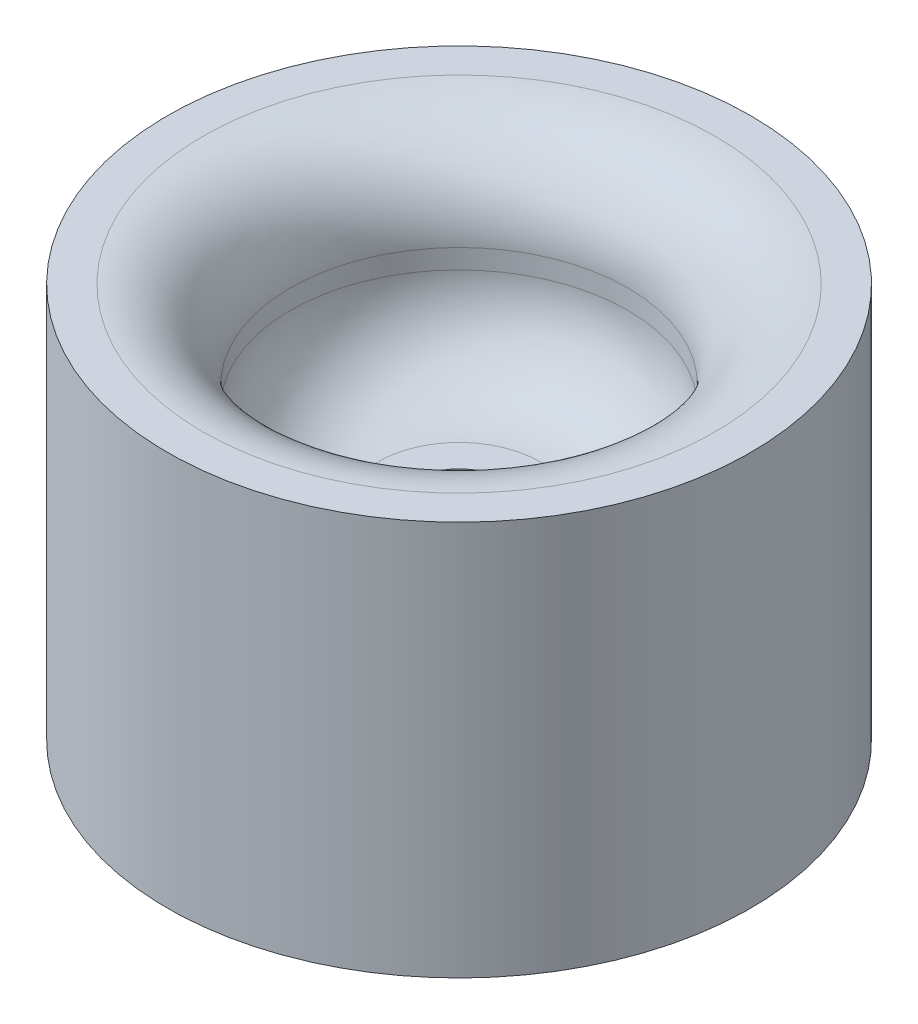
SolidWorks part; units mm, degrees
ref_plane "Front Plane" through (0, 0, 0) normal (0, 0, 1) x (1, 0, 0)
ref_plane "Top Plane" through (0, 0, 0) normal (0, 1, 0) x (1, 0, 0)
ref_plane "Right Plane" through (0, 0, 0) normal (1, 0, 0) x (0, 0, -1)
sketch "Sketch1" plane through (0, 0, 0) normal (1, 0, 0) x (0, 0, -1)
  line L0 (0, 0) -> (0, 76.2)
  line L1 (0, 76.2) -> (-21.1808, 76.2)
  line L2 (-44.0408, 99.06) -> (-44.0408, 104.14)
  line L3 (-66.9008, 127) -> (-76.2, 127)
  line L4 (-76.2, 127) -> (-76.2, 0)
  line L5 (-76.2, 0) -> (0, 0)
  arc A0 (-21.1808, 76.2) -> (-44.0408, 99.06) centre (-21.1808, 99.06) cw
  arc A1 (-44.0408, 104.14) -> (-66.9008, 127) centre (-66.9008, 104.14) ccw
  dimension "D4" = 22.86
  dimension "D1" = 76.2
  dimension "D2" = 127
  dimension "D3" = 76.2
revolve "Revolve1" add sketch "Sketch1" angle 360 about L0
sketch "Sketch2" plane through (0, 76.2, 0) normal (0, 1, 0) x (1, 0, 0)
  circle A0 centre (0, 0) radius 12.7
extrude "Cut-Extrude1" cut sketch "Sketch2" against normal through all
sketch "Sketch3" plane through (0, 0, 0) normal (0, -1, 0) x (-1, 0, 0)
  circle A0 centre (0, 0) radius 76.2
extrude "Cut-Extrude2" cut sketch "Sketch3" against normal blind 23.876
